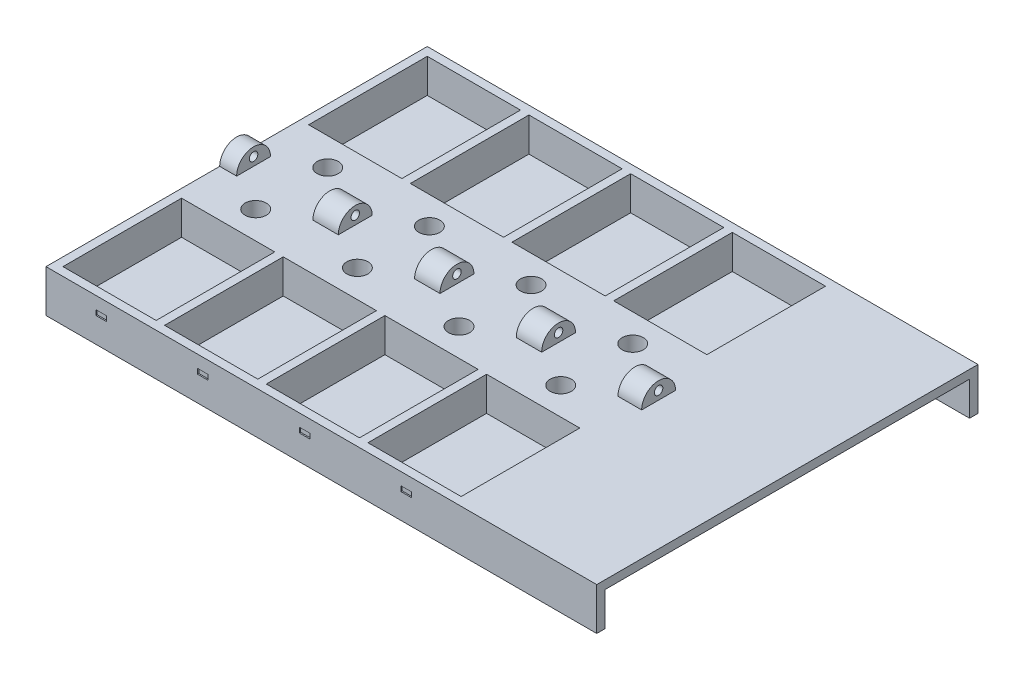
SolidWorks part; units mm, degrees
ref_plane "前视基准面" through (0, 0, 0) normal (0, 0, 1) x (1, 0, 0)
ref_plane "上视基准面" through (0, 0, 0) normal (0, 1, 0) x (1, 0, 0)
ref_plane "右视基准面" through (0, 0, 0) normal (1, 0, 0) x (0, 0, -1)
sketch "草图1" plane through (0, 0, 0) normal (0, 1, 0) x (1, 0, 0)
  line L1 (0, 0) -> (130, 0)
  line L2 (0, 0) -> (0, 90)
  line L3 (0, 90) -> (130, 90)
  line L4 (130, 0) -> (130, 90)
extrude "凸台-拉伸1" add sketch "草图1" along normal blind 10
sketch "草图2" plane through (0, 10, 0) normal (0, 1, 0) x (1, 0, 0)
  line L2 (130, 90) -> (0, 90) construction
  line L3 (2, 88) -> (24, 88)
  line L4 (2, 88) -> (2, 60)
  line L5 (2, 60) -> (24, 60)
  line L6 (24, 88) -> (24, 60)
  line L7 (0, 90) -> (0, 0) construction
  line L12 (26, 60) -> (48, 60)
  line L14 (26, 88) -> (26, 60)
  line L15 (26, 88) -> (48, 88)
  line L16 (48, 88) -> (48, 60)
  line L17 (50, 60) -> (72, 60)
  line L18 (50, 88) -> (50, 60)
  line L19 (50, 88) -> (72, 88)
  line L20 (72, 88) -> (72, 60)
  line L21 (74, 60) -> (96, 60)
  line L22 (74, 88) -> (74, 60)
  line L23 (74, 88) -> (96, 88)
  line L24 (96, 88) -> (96, 60)
  line L25 (26, 2) -> (48, 2)
  line L26 (26, 30) -> (26, 2)
  line L27 (26, 30) -> (48, 30)
  line L28 (48, 30) -> (48, 2)
  line L29 (50, 2) -> (72, 2)
  line L30 (50, 30) -> (50, 2)
  line L31 (50, 30) -> (72, 30)
  line L32 (72, 30) -> (72, 2)
  line L33 (74, 2) -> (96, 2)
  line L34 (74, 30) -> (74, 2)
  line L35 (74, 30) -> (96, 30)
  line L36 (96, 30) -> (96, 2)
  line L37 (2, 2) -> (24, 2)
  line L38 (2, 30) -> (2, 2)
  line L39 (2, 30) -> (24, 30)
  line L40 (24, 30) -> (24, 2)
  dimension "D2" = 2
  dimension "D3" = 2
  dimension "D4" = 4
  dimension "D5" = 2
extrude "切除-拉伸1" cut sketch "草图2" against normal blind 8
sketch "草图3" plane through (0, 0, 0) normal (-1, 0, 0) x (0, 0, 1)
  line L0 (-57.5, 0) -> (-32.5, 0)
  line L1 (-57.5, 0) -> (-57.5, 6)
  line L2 (-32.5, 0) -> (-32.5, 6)
  line L3 (-57.5, 6) -> (-32.5, 6)
extrude "切除-拉伸2" cut sketch "草图3" against normal through all
sketch "草图4" plane through (0, 0, 0) normal (-1, 0, 0) x (0, 0, 1)
  line L1 (-49, 10) -> (-41, 10)
  arc A0 (-41, 10) -> (-49, 10) centre (-45, 10) ccw
extrude "凸台-拉伸2" add sketch "草图4" against normal through all
sketch "草图5" plane through (0, 0, 0) normal (-1, 0, 0) x (0, 0, 1)
  circle A0 centre (-45, 12) radius 1
sketch "草图7" plane through (0, 6, 0) normal (0, -1, 0) x (1, 0, 0)
  circle A0 centre (13, -36.5) radius 2.5
  circle A1 centre (37, -36.5) radius 2.5
  circle A2 centre (61, -36.5) radius 2.5
  circle A3 centre (85, -36.5) radius 2.5
  circle A4 centre (85, -53.5) radius 2.5
  circle A5 centre (61, -53.5) radius 2.5
  circle A6 centre (37, -53.5) radius 2.5
  circle A7 centre (13, -53.5) radius 2.5
  dimension "D1" = 4
extrude "切除-拉伸5" cut sketch "草图7" against normal through all
ref_plane "基准面1" through (4, 0, 0) normal (-1, 0, 0) x (0, 0, 1)
extrude "切除-拉伸6" cut sketch "草图5" against normal through all
sketch "草图8" plane through (4, 0, 0) normal (-1, 0, 0) x (0, 0, 1)
  line L0 (-49, 10) -> (-49, 15.9145)
  line L1 (-49, 15.9145) -> (-40.7618, 15.9145)
  line L2 (-40.7618, 15.9145) -> (-41, 10)
  line L3 (-41, 10) -> (-49, 10)
extrude "切除-拉伸8" cut sketch "草图8" against normal blind 18
sketch "草图9" plane through (0, 10, 0) normal (0, 1, 0) x (1, 0, 0)
  line L0 (-8.6351, 44.8961) -> (147.7746, 44.8961) construction
pattern_linear "阵列(线性)1" count 4 spacing 24 along (1, 0, 0) of "切除-拉伸8"
sketch "草图10" plane through (0, 0, -90) normal (0, 0, -1) x (-1, 0, 0)
  line L4 (-12.9925, 7.1) -> (-11.7925, 7.1)
  line L5 (-11.7925, 7.1) -> (-11.7925, 5.9)
  line L6 (-11.7925, 5.9) -> (-13.0825, 5.9)
  line L7 (-13.0825, 5.9) -> (-14.2825, 5.9)
  line L8 (-14.2825, 5.9) -> (-14.2825, 7.1)
  line L9 (-14.2825, 7.1) -> (-12.9925, 7.1)
extrude "切除-拉伸9" cut sketch "草图10" against normal blind 0.5
pattern_linear "阵列(线性)2" count 4 spacing 24 along (1, 0, 0) of "切除-拉伸9"
ref_plane "基准面2" through (0, 0, -44.8961) normal (0, 0, 1) x (1, 0, 0)
mirror "镜向1" about plane through (0, 0, -44.8961) normal (0, 0, 1) of "阵列(线性)2", "切除-拉伸9"
sketch "草图11" plane through (130, 0, 0) normal (1, 0, 0) x (0, 0, -1)
  line L0 (0, 10) -> (0, 0) construction
  line L1 (0, 0) -> (32.5, 0) construction
  line L2 (2, 0) -> (2, 8)
  line L3 (2, 8) -> (88, 8)
  line L4 (88, 8) -> (88, 0)
  line L5 (57.5, 0) -> (90, 0) construction
  line L6 (88, 0) -> (2, 0)
  dimension "D1" = 86
  dimension "D2" = 2
extrude "切除-拉伸10" cut sketch "草图11" against normal offset from surface (32 mm away) 2 up to face at (96, 6, -16)
sketch "草图12" plane through (0, 10, 0) normal (0, 1, 0) x (1, 0, 0)
  line L0 (99.6044, 41) -> (99.6044, 49)
  line L1 (130, 41) -> (94, 41) construction
  line L2 (130, 49) -> (94, 49) construction
  line L3 (99.6044, 49) -> (130, 49)
  line L4 (130, 49) -> (130, 41)
  line L5 (130, 41) -> (99.6044, 41)
extrude "切除-拉伸11" cut sketch "草图12" along normal blind 8
sketch "草图13" plane through (0, 10, 0) normal (0, 1, 0) x (1, 0, 0)
  line L0 (26, 88) -> (26, 95.3656)
  line L1 (26, 95.3656) -> (150.8446, 95.3656)
  line L2 (150.8446, 95.3656) -> (150.8446, -9.5052)
  line L3 (150.8446, -9.5052) -> (26, -9.5052)
  line L4 (26, -9.5052) -> (26, 88)
